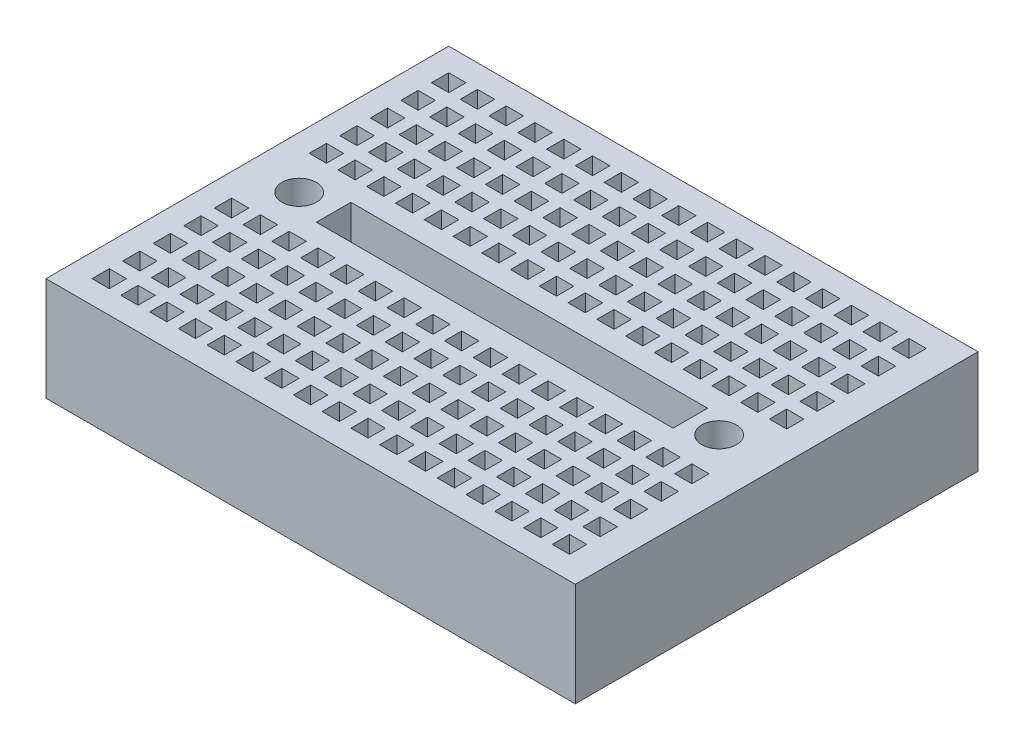
SolidWorks part; units mm, degrees
ref_plane "Front Plane" through (0, 0, 0) normal (0, 0, 1) x (1, 0, 0)
ref_plane "Top Plane" through (0, 0, 0) normal (0, 1, 0) x (1, 0, 0)
ref_plane "Right Plane" through (0, 0, 0) normal (1, 0, 0) x (0, 0, -1)
sketch "Sketch1" plane through (0, 0, 0) normal (0, 1, 0) x (1, 0, 0)
  line L1 (-23, -17.5) -> (23, -17.5)
  line L2 (-23, -17.5) -> (-23, 17.5)
  line L3 (-23, 17.5) -> (23, 17.5)
  line L4 (23, -17.5) -> (23, 17.5)
  point P0 (0, 0)
  dimension "D1" = 46
  dimension "D2" = 35
extrude "Boss-Extrude1" add sketch "Sketch1" along normal blind 9
sketch "Sketch2" plane through (0, 9, 0) normal (0, 1, 0) x (1, 0, 0)
  line L1 (-19.5, 15.5) -> (-21, 15.5)
  line L2 (-21, 15.5) -> (-21, 14)
  line L4 (-15.5, -1.5) -> (15.5, -1.5)
  line L12 (-19.5, 15.5) -> (-19.5, 14)
  line L13 (-19.5, 14) -> (-21, 14)
  line L16 (-17, 15.5) -> (-18.5, 15.5)
  line L17 (-18.5, 15.5) -> (-18.5, 14)
  line L18 (-17, 14) -> (-18.5, 14)
  line L19 (-17, 15.5) -> (-17, 14)
  line L20 (-14.5, 15.5) -> (-16, 15.5)
  line L21 (-16, 15.5) -> (-16, 14)
  line L22 (-14.5, 14) -> (-16, 14)
  line L23 (-14.5, 15.5) -> (-14.5, 14)
  line L24 (-12, 15.5) -> (-13.5, 15.5)
  line L25 (-13.5, 15.5) -> (-13.5, 14)
  line L26 (-12, 14) -> (-13.5, 14)
  line L27 (-12, 15.5) -> (-12, 14)
  line L28 (-9.5, 15.5) -> (-11, 15.5)
  line L29 (-11, 15.5) -> (-11, 14)
  line L30 (-9.5, 14) -> (-11, 14)
  line L31 (-9.5, 15.5) -> (-9.5, 14)
  line L32 (-7, 15.5) -> (-8.5, 15.5)
  line L33 (-8.5, 15.5) -> (-8.5, 14)
  line L34 (-7, 14) -> (-8.5, 14)
  line L35 (-7, 15.5) -> (-7, 14)
  line L36 (-4.5, 15.5) -> (-6, 15.5)
  line L37 (-6, 15.5) -> (-6, 14)
  line L38 (-4.5, 14) -> (-6, 14)
  line L39 (-4.5, 15.5) -> (-4.5, 14)
  line L40 (-2, 15.5) -> (-3.5, 15.5)
  line L41 (-3.5, 15.5) -> (-3.5, 14)
  line L42 (-2, 14) -> (-3.5, 14)
  line L43 (-2, 15.5) -> (-2, 14)
  line L44 (0.5, 15.5) -> (-1, 15.5)
  line L45 (-1, 15.5) -> (-1, 14)
  line L46 (0.5, 14) -> (-1, 14)
  line L47 (0.5, 15.5) -> (0.5, 14)
  line L48 (3, 15.5) -> (1.5, 15.5)
  line L49 (1.5, 15.5) -> (1.5, 14)
  line L50 (3, 14) -> (1.5, 14)
  line L51 (3, 15.5) -> (3, 14)
  line L52 (5.5, 15.5) -> (4, 15.5)
  line L53 (4, 15.5) -> (4, 14)
  line L54 (5.5, 14) -> (4, 14)
  line L55 (5.5, 15.5) -> (5.5, 14)
  line L56 (8, 15.5) -> (6.5, 15.5)
  line L57 (6.5, 15.5) -> (6.5, 14)
  line L58 (8, 14) -> (6.5, 14)
  line L59 (8, 15.5) -> (8, 14)
  line L60 (10.5, 15.5) -> (9, 15.5)
  line L61 (9, 15.5) -> (9, 14)
  line L62 (10.5, 14) -> (9, 14)
  line L63 (10.5, 15.5) -> (10.5, 14)
  line L64 (13, 15.5) -> (11.5, 15.5)
  line L65 (11.5, 15.5) -> (11.5, 14)
  line L66 (13, 14) -> (11.5, 14)
  line L67 (13, 15.5) -> (13, 14)
  line L68 (15.5, 15.5) -> (14, 15.5)
  line L69 (14, 15.5) -> (14, 14)
  line L70 (15.5, 14) -> (14, 14)
  line L71 (15.5, 15.5) -> (15.5, 14)
  line L72 (18, 15.5) -> (16.5, 15.5)
  line L73 (16.5, 15.5) -> (16.5, 14)
  line L74 (18, 14) -> (16.5, 14)
  line L75 (18, 15.5) -> (18, 14)
  line L76 (20.5, 15.5) -> (19, 15.5)
  line L77 (19, 15.5) -> (19, 14)
  line L78 (20.5, 14) -> (19, 14)
  line L79 (20.5, 15.5) -> (20.5, 14)
  line L80 (-17, 12.8426) -> (-18.5, 12.8426)
  line L81 (-18.5, 12.8426) -> (-18.5, 11.3426)
  line L82 (-17, 11.3426) -> (-18.5, 11.3426)
  line L83 (-17, 12.8426) -> (-17, 11.3426)
  line L84 (-14.5, 12.8426) -> (-16, 12.8426)
  line L85 (-16, 12.8426) -> (-16, 11.3426)
  line L86 (-14.5, 11.3426) -> (-16, 11.3426)
  line L87 (-14.5, 12.8426) -> (-14.5, 11.3426)
  line L88 (-12, 12.8426) -> (-13.5, 12.8426)
  line L89 (-13.5, 12.8426) -> (-13.5, 11.3426)
  line L90 (-12, 11.3426) -> (-13.5, 11.3426)
  line L91 (-12, 12.8426) -> (-12, 11.3426)
  line L92 (-9.5, 12.8426) -> (-11, 12.8426)
  line L93 (-11, 12.8426) -> (-11, 11.3426)
  line L94 (-9.5, 11.3426) -> (-11, 11.3426)
  line L95 (-9.5, 12.8426) -> (-9.5, 11.3426)
  line L96 (-7, 12.8426) -> (-8.5, 12.8426)
  line L97 (-8.5, 12.8426) -> (-8.5, 11.3426)
  line L98 (-7, 11.3426) -> (-8.5, 11.3426)
  line L99 (-7, 12.8426) -> (-7, 11.3426)
  line L100 (-4.5, 12.8426) -> (-6, 12.8426)
  line L101 (-6, 12.8426) -> (-6, 11.3426)
  line L102 (-4.5, 11.3426) -> (-6, 11.3426)
  line L103 (-4.5, 12.8426) -> (-4.5, 11.3426)
  line L104 (-2, 12.8426) -> (-3.5, 12.8426)
  line L105 (-3.5, 12.8426) -> (-3.5, 11.3426)
  line L106 (-2, 11.3426) -> (-3.5, 11.3426)
  line L107 (-2, 12.8426) -> (-2, 11.3426)
  line L108 (0.5, 12.8426) -> (-1, 12.8426)
  line L109 (-1, 12.8426) -> (-1, 11.3426)
  line L110 (0.5, 11.3426) -> (-1, 11.3426)
  line L111 (0.5, 12.8426) -> (0.5, 11.3426)
  line L112 (3, 12.8426) -> (1.5, 12.8426)
  line L113 (1.5, 12.8426) -> (1.5, 11.3426)
  line L114 (3, 11.3426) -> (1.5, 11.3426)
  line L115 (3, 12.8426) -> (3, 11.3426)
  line L116 (5.5, 12.8426) -> (4, 12.8426)
  line L117 (4, 12.8426) -> (4, 11.3426)
  line L118 (5.5, 11.3426) -> (4, 11.3426)
  line L119 (5.5, 12.8426) -> (5.5, 11.3426)
  line L120 (8, 12.8426) -> (6.5, 12.8426)
  line L121 (6.5, 12.8426) -> (6.5, 11.3426)
  line L122 (8, 11.3426) -> (6.5, 11.3426)
  line L123 (8, 12.8426) -> (8, 11.3426)
  line L124 (10.5, 12.8426) -> (9, 12.8426)
  line L125 (9, 12.8426) -> (9, 11.3426)
  line L126 (10.5, 11.3426) -> (9, 11.3426)
  line L127 (10.5, 12.8426) -> (10.5, 11.3426)
  line L128 (13, 12.8426) -> (11.5, 12.8426)
  line L129 (11.5, 12.8426) -> (11.5, 11.3426)
  line L130 (13, 11.3426) -> (11.5, 11.3426)
  line L131 (13, 12.8426) -> (13, 11.3426)
  line L132 (15.5, 12.8426) -> (14, 12.8426)
  line L133 (14, 12.8426) -> (14, 11.3426)
  line L134 (15.5, 11.3426) -> (14, 11.3426)
  line L135 (15.5, 12.8426) -> (15.5, 11.3426)
  line L136 (18, 12.8426) -> (16.5, 12.8426)
  line L137 (16.5, 12.8426) -> (16.5, 11.3426)
  line L138 (18, 11.3426) -> (16.5, 11.3426)
  line L139 (18, 12.8426) -> (18, 11.3426)
  line L140 (20.5, 12.8426) -> (19, 12.8426)
  line L141 (19, 12.8426) -> (19, 11.3426)
  line L142 (20.5, 11.3426) -> (19, 11.3426)
  line L143 (20.5, 12.8426) -> (20.5, 11.3426)
  line L144 (-17, 10.1851) -> (-18.5, 10.1851)
  line L145 (-18.5, 10.1851) -> (-18.5, 8.6851)
  line L146 (-17, 8.6851) -> (-18.5, 8.6851)
  line L147 (-17, 10.1851) -> (-17, 8.6851)
  line L148 (-14.5, 10.1851) -> (-16, 10.1851)
  line L149 (-16, 10.1851) -> (-16, 8.6851)
  line L150 (-14.5, 8.6851) -> (-16, 8.6851)
  line L151 (-14.5, 10.1851) -> (-14.5, 8.6851)
  line L152 (-12, 10.1851) -> (-13.5, 10.1851)
  line L153 (-13.5, 10.1851) -> (-13.5, 8.6851)
  line L154 (-12, 8.6851) -> (-13.5, 8.6851)
  line L155 (-12, 10.1851) -> (-12, 8.6851)
  line L156 (-9.5, 10.1851) -> (-11, 10.1851)
  line L157 (-11, 10.1851) -> (-11, 8.6851)
  line L158 (-9.5, 8.6851) -> (-11, 8.6851)
  line L159 (-9.5, 10.1851) -> (-9.5, 8.6851)
  line L160 (-7, 10.1851) -> (-8.5, 10.1851)
  line L161 (-8.5, 10.1851) -> (-8.5, 8.6851)
  line L162 (-7, 8.6851) -> (-8.5, 8.6851)
  line L163 (-7, 10.1851) -> (-7, 8.6851)
  line L164 (-4.5, 10.1851) -> (-6, 10.1851)
  line L165 (-6, 10.1851) -> (-6, 8.6851)
  line L166 (-4.5, 8.6851) -> (-6, 8.6851)
  line L167 (-4.5, 10.1851) -> (-4.5, 8.6851)
  line L168 (-2, 10.1851) -> (-3.5, 10.1851)
  line L169 (-3.5, 10.1851) -> (-3.5, 8.6851)
  line L170 (-2, 8.6851) -> (-3.5, 8.6851)
  line L171 (-2, 10.1851) -> (-2, 8.6851)
  line L172 (0.5, 10.1851) -> (-1, 10.1851)
  line L173 (-1, 10.1851) -> (-1, 8.6851)
  line L174 (0.5, 8.6851) -> (-1, 8.6851)
  line L175 (0.5, 10.1851) -> (0.5, 8.6851)
  line L176 (3, 10.1851) -> (1.5, 10.1851)
  line L177 (1.5, 10.1851) -> (1.5, 8.6851)
  line L178 (3, 8.6851) -> (1.5, 8.6851)
  line L179 (3, 10.1851) -> (3, 8.6851)
  line L180 (5.5, 10.1851) -> (4, 10.1851)
  line L181 (4, 10.1851) -> (4, 8.6851)
  line L182 (5.5, 8.6851) -> (4, 8.6851)
  line L183 (5.5, 10.1851) -> (5.5, 8.6851)
  line L184 (8, 10.1851) -> (6.5, 10.1851)
  line L185 (6.5, 10.1851) -> (6.5, 8.6851)
  line L186 (8, 8.6851) -> (6.5, 8.6851)
  line L187 (8, 10.1851) -> (8, 8.6851)
  line L188 (10.5, 10.1851) -> (9, 10.1851)
  line L189 (9, 10.1851) -> (9, 8.6851)
  line L190 (10.5, 8.6851) -> (9, 8.6851)
  line L191 (10.5, 10.1851) -> (10.5, 8.6851)
  line L192 (13, 10.1851) -> (11.5, 10.1851)
  line L193 (11.5, 10.1851) -> (11.5, 8.6851)
  line L194 (13, 8.6851) -> (11.5, 8.6851)
  line L195 (13, 10.1851) -> (13, 8.6851)
  line L196 (15.5, 10.1851) -> (14, 10.1851)
  line L197 (14, 10.1851) -> (14, 8.6851)
  line L198 (15.5, 8.6851) -> (14, 8.6851)
  line L199 (15.5, 10.1851) -> (15.5, 8.6851)
  line L200 (18, 10.1851) -> (16.5, 10.1851)
  line L201 (16.5, 10.1851) -> (16.5, 8.6851)
  line L202 (18, 8.6851) -> (16.5, 8.6851)
  line L203 (18, 10.1851) -> (18, 8.6851)
  line L204 (20.5, 10.1851) -> (19, 10.1851)
  line L205 (19, 10.1851) -> (19, 8.6851)
  line L206 (20.5, 8.6851) -> (19, 8.6851)
  line L207 (20.5, 10.1851) -> (20.5, 8.6851)
  line L208 (-17, 7.5277) -> (-18.5, 7.5277)
  line L209 (-18.5, 7.5277) -> (-18.5, 6.0277)
  line L210 (-17, 6.0277) -> (-18.5, 6.0277)
  line L211 (-17, 7.5277) -> (-17, 6.0277)
  line L212 (-14.5, 7.5277) -> (-16, 7.5277)
  line L213 (-16, 7.5277) -> (-16, 6.0277)
  line L214 (-14.5, 6.0277) -> (-16, 6.0277)
  line L215 (-14.5, 7.5277) -> (-14.5, 6.0277)
  line L216 (-12, 7.5277) -> (-13.5, 7.5277)
  line L217 (-13.5, 7.5277) -> (-13.5, 6.0277)
  line L218 (-12, 6.0277) -> (-13.5, 6.0277)
  line L219 (-12, 7.5277) -> (-12, 6.0277)
  line L220 (-9.5, 7.5277) -> (-11, 7.5277)
  line L221 (-11, 7.5277) -> (-11, 6.0277)
  line L222 (-9.5, 6.0277) -> (-11, 6.0277)
  line L223 (-9.5, 7.5277) -> (-9.5, 6.0277)
  line L224 (-7, 7.5277) -> (-8.5, 7.5277)
  line L225 (-8.5, 7.5277) -> (-8.5, 6.0277)
  line L226 (-7, 6.0277) -> (-8.5, 6.0277)
  line L227 (-7, 7.5277) -> (-7, 6.0277)
  line L228 (-4.5, 7.5277) -> (-6, 7.5277)
  line L229 (-6, 7.5277) -> (-6, 6.0277)
  line L230 (-4.5, 6.0277) -> (-6, 6.0277)
  line L231 (-4.5, 7.5277) -> (-4.5, 6.0277)
  line L232 (-2, 7.5277) -> (-3.5, 7.5277)
  line L233 (-3.5, 7.5277) -> (-3.5, 6.0277)
  line L234 (-2, 6.0277) -> (-3.5, 6.0277)
  line L235 (-2, 7.5277) -> (-2, 6.0277)
  line L236 (0.5, 7.5277) -> (-1, 7.5277)
  line L237 (-1, 7.5277) -> (-1, 6.0277)
  line L238 (0.5, 6.0277) -> (-1, 6.0277)
  line L239 (0.5, 7.5277) -> (0.5, 6.0277)
  line L240 (3, 7.5277) -> (1.5, 7.5277)
  line L241 (1.5, 7.5277) -> (1.5, 6.0277)
  line L242 (3, 6.0277) -> (1.5, 6.0277)
  line L243 (3, 7.5277) -> (3, 6.0277)
  line L244 (5.5, 7.5277) -> (4, 7.5277)
  line L245 (4, 7.5277) -> (4, 6.0277)
  line L246 (5.5, 6.0277) -> (4, 6.0277)
  line L247 (5.5, 7.5277) -> (5.5, 6.0277)
  line L248 (8, 7.5277) -> (6.5, 7.5277)
  line L249 (6.5, 7.5277) -> (6.5, 6.0277)
  line L250 (8, 6.0277) -> (6.5, 6.0277)
  line L251 (8, 7.5277) -> (8, 6.0277)
  line L252 (10.5, 7.5277) -> (9, 7.5277)
  line L253 (9, 7.5277) -> (9, 6.0277)
  line L254 (10.5, 6.0277) -> (9, 6.0277)
  line L255 (10.5, 7.5277) -> (10.5, 6.0277)
  line L256 (13, 7.5277) -> (11.5, 7.5277)
  line L257 (11.5, 7.5277) -> (11.5, 6.0277)
  line L258 (13, 6.0277) -> (11.5, 6.0277)
  line L259 (13, 7.5277) -> (13, 6.0277)
  line L260 (15.5, 7.5277) -> (14, 7.5277)
  line L261 (14, 7.5277) -> (14, 6.0277)
  line L262 (15.5, 6.0277) -> (14, 6.0277)
  line L263 (15.5, 7.5277) -> (15.5, 6.0277)
  line L264 (18, 7.5277) -> (16.5, 7.5277)
  line L265 (16.5, 7.5277) -> (16.5, 6.0277)
  line L266 (18, 6.0277) -> (16.5, 6.0277)
  line L267 (18, 7.5277) -> (18, 6.0277)
  line L268 (20.5, 7.5277) -> (19, 7.5277)
  line L269 (19, 7.5277) -> (19, 6.0277)
  line L270 (20.5, 6.0277) -> (19, 6.0277)
  line L271 (20.5, 7.5277) -> (20.5, 6.0277)
  line L272 (-17, 4.8702) -> (-18.5, 4.8702)
  line L273 (-18.5, 4.8702) -> (-18.5, 3.3702)
  line L274 (-17, 3.3702) -> (-18.5, 3.3702)
  line L275 (-17, 4.8702) -> (-17, 3.3702)
  line L276 (-14.5, 4.8702) -> (-16, 4.8702)
  line L277 (-16, 4.8702) -> (-16, 3.3702)
  line L278 (-14.5, 3.3702) -> (-16, 3.3702)
  line L279 (-14.5, 4.8702) -> (-14.5, 3.3702)
  line L280 (-12, 4.8702) -> (-13.5, 4.8702)
  line L281 (-13.5, 4.8702) -> (-13.5, 3.3702)
  line L282 (-12, 3.3702) -> (-13.5, 3.3702)
  line L283 (-12, 4.8702) -> (-12, 3.3702)
  line L284 (-9.5, 4.8702) -> (-11, 4.8702)
  line L285 (-11, 4.8702) -> (-11, 3.3702)
  line L286 (-9.5, 3.3702) -> (-11, 3.3702)
  line L287 (-9.5, 4.8702) -> (-9.5, 3.3702)
  line L288 (-7, 4.8702) -> (-8.5, 4.8702)
  line L289 (-8.5, 4.8702) -> (-8.5, 3.3702)
  line L290 (-7, 3.3702) -> (-8.5, 3.3702)
  line L291 (-7, 4.8702) -> (-7, 3.3702)
  line L292 (-4.5, 4.8702) -> (-6, 4.8702)
  line L293 (-6, 4.8702) -> (-6, 3.3702)
  line L294 (-4.5, 3.3702) -> (-6, 3.3702)
  line L295 (-4.5, 4.8702) -> (-4.5, 3.3702)
  line L296 (-2, 4.8702) -> (-3.5, 4.8702)
  line L297 (-3.5, 4.8702) -> (-3.5, 3.3702)
  line L298 (-2, 3.3702) -> (-3.5, 3.3702)
  line L299 (-2, 4.8702) -> (-2, 3.3702)
  line L300 (0.5, 4.8702) -> (-1, 4.8702)
  line L301 (-1, 4.8702) -> (-1, 3.3702)
  line L302 (0.5, 3.3702) -> (-1, 3.3702)
  line L303 (0.5, 4.8702) -> (0.5, 3.3702)
  line L304 (3, 4.8702) -> (1.5, 4.8702)
  line L305 (1.5, 4.8702) -> (1.5, 3.3702)
  line L306 (3, 3.3702) -> (1.5, 3.3702)
  line L307 (3, 4.8702) -> (3, 3.3702)
  line L308 (5.5, 4.8702) -> (4, 4.8702)
  line L309 (4, 4.8702) -> (4, 3.3702)
  line L310 (5.5, 3.3702) -> (4, 3.3702)
  line L311 (5.5, 4.8702) -> (5.5, 3.3702)
  line L312 (8, 4.8702) -> (6.5, 4.8702)
  line L313 (6.5, 4.8702) -> (6.5, 3.3702)
  line L314 (8, 3.3702) -> (6.5, 3.3702)
  line L315 (8, 4.8702) -> (8, 3.3702)
  line L316 (10.5, 4.8702) -> (9, 4.8702)
  line L317 (9, 4.8702) -> (9, 3.3702)
  line L318 (10.5, 3.3702) -> (9, 3.3702)
  line L319 (10.5, 4.8702) -> (10.5, 3.3702)
  line L320 (13, 4.8702) -> (11.5, 4.8702)
  line L321 (11.5, 4.8702) -> (11.5, 3.3702)
  line L322 (13, 3.3702) -> (11.5, 3.3702)
  line L323 (13, 4.8702) -> (13, 3.3702)
  line L324 (15.5, 4.8702) -> (14, 4.8702)
  line L325 (14, 4.8702) -> (14, 3.3702)
  line L326 (15.5, 3.3702) -> (14, 3.3702)
  line L327 (15.5, 4.8702) -> (15.5, 3.3702)
  line L328 (18, 4.8702) -> (16.5, 4.8702)
  line L329 (16.5, 4.8702) -> (16.5, 3.3702)
  line L330 (18, 3.3702) -> (16.5, 3.3702)
  line L331 (18, 4.8702) -> (18, 3.3702)
  line L332 (20.5, 4.8702) -> (19, 4.8702)
  line L333 (19, 4.8702) -> (19, 3.3702)
  line L334 (20.5, 3.3702) -> (19, 3.3702)
  line L335 (20.5, 4.8702) -> (20.5, 3.3702)
  line L336 (-19.5, 12.8426) -> (-21, 12.8426)
  line L337 (-21, 12.8426) -> (-21, 11.3426)
  line L338 (-19.5, 11.3426) -> (-21, 11.3426)
  line L339 (-19.5, 12.8426) -> (-19.5, 11.3426)
  line L340 (-19.5, 10.1851) -> (-21, 10.1851)
  line L341 (-21, 10.1851) -> (-21, 8.6851)
  line L342 (-19.5, 8.6851) -> (-21, 8.6851)
  line L343 (-19.5, 10.1851) -> (-19.5, 8.6851)
  line L344 (-19.5, 7.5277) -> (-21, 7.5277)
  line L345 (-21, 7.5277) -> (-21, 6.0277)
  line L346 (-19.5, 6.0277) -> (-21, 6.0277)
  line L347 (-19.5, 7.5277) -> (-19.5, 6.0277)
  line L348 (-19.5, 4.8702) -> (-21, 4.8702)
  line L349 (-21, 4.8702) -> (-21, 3.3702)
  line L350 (-19.5, 3.3702) -> (-21, 3.3702)
  line L351 (-19.5, 4.8702) -> (-19.5, 3.3702)
  line L356 (-15.5, -1.5) -> (-15.5, 1.5)
  line L357 (-15.5, 1.5) -> (15.5, 1.5)
  line L358 (15.5, -1.5) -> (15.5, 1.5)
  line L363 (-19.5, -4.8702) -> (-19.5, -3.3702)
  line L364 (-19.5, -3.3702) -> (-21, -3.3702)
  line L365 (-21, -4.8702) -> (-21, -3.3702)
  line L366 (-19.5, -4.8702) -> (-21, -4.8702)
  line L367 (-19.5, -7.5277) -> (-19.5, -6.0277)
  line L368 (-19.5, -6.0277) -> (-21, -6.0277)
  line L369 (-21, -7.5277) -> (-21, -6.0277)
  line L370 (-19.5, -7.5277) -> (-21, -7.5277)
  line L371 (-19.5, -10.1851) -> (-19.5, -8.6851)
  line L372 (-19.5, -8.6851) -> (-21, -8.6851)
  line L373 (-21, -10.1851) -> (-21, -8.6851)
  line L374 (-19.5, -10.1851) -> (-21, -10.1851)
  line L375 (-19.5, -12.8426) -> (-19.5, -11.3426)
  line L376 (-19.5, -11.3426) -> (-21, -11.3426)
  line L377 (-21, -12.8426) -> (-21, -11.3426)
  line L378 (-19.5, -12.8426) -> (-21, -12.8426)
  line L379 (20.5, -4.8702) -> (20.5, -3.3702)
  line L380 (20.5, -3.3702) -> (19, -3.3702)
  line L381 (19, -4.8702) -> (19, -3.3702)
  line L382 (20.5, -4.8702) -> (19, -4.8702)
  line L383 (18, -4.8702) -> (18, -3.3702)
  line L384 (18, -3.3702) -> (16.5, -3.3702)
  line L385 (16.5, -4.8702) -> (16.5, -3.3702)
  line L386 (18, -4.8702) -> (16.5, -4.8702)
  line L387 (15.5, -4.8702) -> (15.5, -3.3702)
  line L388 (15.5, -3.3702) -> (14, -3.3702)
  line L389 (14, -4.8702) -> (14, -3.3702)
  line L390 (15.5, -4.8702) -> (14, -4.8702)
  line L391 (13, -4.8702) -> (13, -3.3702)
  line L392 (13, -3.3702) -> (11.5, -3.3702)
  line L393 (11.5, -4.8702) -> (11.5, -3.3702)
  line L394 (13, -4.8702) -> (11.5, -4.8702)
  line L395 (10.5, -4.8702) -> (10.5, -3.3702)
  line L396 (10.5, -3.3702) -> (9, -3.3702)
  line L397 (9, -4.8702) -> (9, -3.3702)
  line L398 (10.5, -4.8702) -> (9, -4.8702)
  line L399 (8, -4.8702) -> (8, -3.3702)
  line L400 (8, -3.3702) -> (6.5, -3.3702)
  line L401 (6.5, -4.8702) -> (6.5, -3.3702)
  line L402 (8, -4.8702) -> (6.5, -4.8702)
  line L403 (5.5, -4.8702) -> (5.5, -3.3702)
  line L404 (5.5, -3.3702) -> (4, -3.3702)
  line L405 (4, -4.8702) -> (4, -3.3702)
  line L406 (5.5, -4.8702) -> (4, -4.8702)
  line L407 (3, -4.8702) -> (3, -3.3702)
  line L408 (3, -3.3702) -> (1.5, -3.3702)
  line L409 (1.5, -4.8702) -> (1.5, -3.3702)
  line L410 (3, -4.8702) -> (1.5, -4.8702)
  line L411 (0.5, -4.8702) -> (0.5, -3.3702)
  line L412 (0.5, -3.3702) -> (-1, -3.3702)
  line L413 (-1, -4.8702) -> (-1, -3.3702)
  line L414 (0.5, -4.8702) -> (-1, -4.8702)
  line L415 (-2, -4.8702) -> (-2, -3.3702)
  line L416 (-2, -3.3702) -> (-3.5, -3.3702)
  line L417 (-3.5, -4.8702) -> (-3.5, -3.3702)
  line L418 (-2, -4.8702) -> (-3.5, -4.8702)
  line L419 (-4.5, -4.8702) -> (-4.5, -3.3702)
  line L420 (-4.5, -3.3702) -> (-6, -3.3702)
  line L421 (-6, -4.8702) -> (-6, -3.3702)
  line L422 (-4.5, -4.8702) -> (-6, -4.8702)
  line L423 (-7, -4.8702) -> (-7, -3.3702)
  line L424 (-7, -3.3702) -> (-8.5, -3.3702)
  line L425 (-8.5, -4.8702) -> (-8.5, -3.3702)
  line L426 (-7, -4.8702) -> (-8.5, -4.8702)
  line L427 (-9.5, -4.8702) -> (-9.5, -3.3702)
  line L428 (-9.5, -3.3702) -> (-11, -3.3702)
  line L429 (-11, -4.8702) -> (-11, -3.3702)
  line L430 (-9.5, -4.8702) -> (-11, -4.8702)
  line L431 (-12, -4.8702) -> (-12, -3.3702)
  line L432 (-12, -3.3702) -> (-13.5, -3.3702)
  line L433 (-13.5, -4.8702) -> (-13.5, -3.3702)
  line L434 (-12, -4.8702) -> (-13.5, -4.8702)
  line L435 (-14.5, -4.8702) -> (-14.5, -3.3702)
  line L436 (-14.5, -3.3702) -> (-16, -3.3702)
  line L437 (-16, -4.8702) -> (-16, -3.3702)
  line L438 (-14.5, -4.8702) -> (-16, -4.8702)
  line L439 (-17, -4.8702) -> (-17, -3.3702)
  line L440 (-17, -3.3702) -> (-18.5, -3.3702)
  line L441 (-18.5, -4.8702) -> (-18.5, -3.3702)
  line L442 (-17, -4.8702) -> (-18.5, -4.8702)
  line L443 (20.5, -7.5277) -> (20.5, -6.0277)
  line L444 (20.5, -6.0277) -> (19, -6.0277)
  line L445 (19, -7.5277) -> (19, -6.0277)
  line L446 (20.5, -7.5277) -> (19, -7.5277)
  line L447 (18, -7.5277) -> (18, -6.0277)
  line L448 (18, -6.0277) -> (16.5, -6.0277)
  line L449 (16.5, -7.5277) -> (16.5, -6.0277)
  line L450 (18, -7.5277) -> (16.5, -7.5277)
  line L451 (15.5, -7.5277) -> (15.5, -6.0277)
  line L452 (15.5, -6.0277) -> (14, -6.0277)
  line L453 (14, -7.5277) -> (14, -6.0277)
  line L454 (15.5, -7.5277) -> (14, -7.5277)
  line L455 (13, -7.5277) -> (13, -6.0277)
  line L456 (13, -6.0277) -> (11.5, -6.0277)
  line L457 (11.5, -7.5277) -> (11.5, -6.0277)
  line L458 (13, -7.5277) -> (11.5, -7.5277)
  line L459 (10.5, -7.5277) -> (10.5, -6.0277)
  line L460 (10.5, -6.0277) -> (9, -6.0277)
  line L461 (9, -7.5277) -> (9, -6.0277)
  line L462 (10.5, -7.5277) -> (9, -7.5277)
  line L463 (8, -7.5277) -> (8, -6.0277)
  line L464 (8, -6.0277) -> (6.5, -6.0277)
  line L465 (6.5, -7.5277) -> (6.5, -6.0277)
  line L466 (8, -7.5277) -> (6.5, -7.5277)
  line L467 (5.5, -7.5277) -> (5.5, -6.0277)
  line L468 (5.5, -6.0277) -> (4, -6.0277)
  line L469 (4, -7.5277) -> (4, -6.0277)
  line L470 (5.5, -7.5277) -> (4, -7.5277)
  line L471 (3, -7.5277) -> (3, -6.0277)
  line L472 (3, -6.0277) -> (1.5, -6.0277)
  line L473 (1.5, -7.5277) -> (1.5, -6.0277)
  line L474 (3, -7.5277) -> (1.5, -7.5277)
  line L475 (0.5, -7.5277) -> (0.5, -6.0277)
  line L476 (0.5, -6.0277) -> (-1, -6.0277)
  line L477 (-1, -7.5277) -> (-1, -6.0277)
  line L478 (0.5, -7.5277) -> (-1, -7.5277)
  line L479 (-2, -7.5277) -> (-2, -6.0277)
  line L480 (-2, -6.0277) -> (-3.5, -6.0277)
  line L481 (-3.5, -7.5277) -> (-3.5, -6.0277)
  line L482 (-2, -7.5277) -> (-3.5, -7.5277)
  line L483 (-4.5, -7.5277) -> (-4.5, -6.0277)
  line L484 (-4.5, -6.0277) -> (-6, -6.0277)
  line L485 (-6, -7.5277) -> (-6, -6.0277)
  line L486 (-4.5, -7.5277) -> (-6, -7.5277)
  line L487 (-7, -7.5277) -> (-7, -6.0277)
  line L488 (-7, -6.0277) -> (-8.5, -6.0277)
  line L489 (-8.5, -7.5277) -> (-8.5, -6.0277)
  line L490 (-7, -7.5277) -> (-8.5, -7.5277)
  line L491 (-9.5, -7.5277) -> (-9.5, -6.0277)
  line L492 (-9.5, -6.0277) -> (-11, -6.0277)
  line L493 (-11, -7.5277) -> (-11, -6.0277)
  line L494 (-9.5, -7.5277) -> (-11, -7.5277)
  line L495 (-12, -7.5277) -> (-12, -6.0277)
  line L496 (-12, -6.0277) -> (-13.5, -6.0277)
  line L497 (-13.5, -7.5277) -> (-13.5, -6.0277)
  line L498 (-12, -7.5277) -> (-13.5, -7.5277)
  line L499 (-14.5, -7.5277) -> (-14.5, -6.0277)
  line L500 (-14.5, -6.0277) -> (-16, -6.0277)
  line L501 (-16, -7.5277) -> (-16, -6.0277)
  line L502 (-14.5, -7.5277) -> (-16, -7.5277)
  line L503 (-17, -7.5277) -> (-17, -6.0277)
  line L504 (-17, -6.0277) -> (-18.5, -6.0277)
  line L505 (-18.5, -7.5277) -> (-18.5, -6.0277)
  line L506 (-17, -7.5277) -> (-18.5, -7.5277)
  line L507 (20.5, -10.1851) -> (20.5, -8.6851)
  line L508 (20.5, -8.6851) -> (19, -8.6851)
  line L509 (19, -10.1851) -> (19, -8.6851)
  line L510 (20.5, -10.1851) -> (19, -10.1851)
  line L511 (18, -10.1851) -> (18, -8.6851)
  line L512 (18, -8.6851) -> (16.5, -8.6851)
  line L513 (16.5, -10.1851) -> (16.5, -8.6851)
  line L514 (18, -10.1851) -> (16.5, -10.1851)
  line L515 (15.5, -10.1851) -> (15.5, -8.6851)
  line L516 (15.5, -8.6851) -> (14, -8.6851)
  line L517 (14, -10.1851) -> (14, -8.6851)
  line L518 (15.5, -10.1851) -> (14, -10.1851)
  line L519 (13, -10.1851) -> (13, -8.6851)
  line L520 (13, -8.6851) -> (11.5, -8.6851)
  line L521 (11.5, -10.1851) -> (11.5, -8.6851)
  line L522 (13, -10.1851) -> (11.5, -10.1851)
  line L523 (10.5, -10.1851) -> (10.5, -8.6851)
  line L524 (10.5, -8.6851) -> (9, -8.6851)
  line L525 (9, -10.1851) -> (9, -8.6851)
  line L526 (10.5, -10.1851) -> (9, -10.1851)
  line L527 (8, -10.1851) -> (8, -8.6851)
  line L528 (8, -8.6851) -> (6.5, -8.6851)
  line L529 (6.5, -10.1851) -> (6.5, -8.6851)
  line L530 (8, -10.1851) -> (6.5, -10.1851)
  line L531 (5.5, -10.1851) -> (5.5, -8.6851)
  line L532 (5.5, -8.6851) -> (4, -8.6851)
  line L533 (4, -10.1851) -> (4, -8.6851)
  line L534 (5.5, -10.1851) -> (4, -10.1851)
  line L535 (3, -10.1851) -> (3, -8.6851)
  line L536 (3, -8.6851) -> (1.5, -8.6851)
  line L537 (1.5, -10.1851) -> (1.5, -8.6851)
  line L538 (3, -10.1851) -> (1.5, -10.1851)
  line L539 (0.5, -10.1851) -> (0.5, -8.6851)
  line L540 (0.5, -8.6851) -> (-1, -8.6851)
  line L541 (-1, -10.1851) -> (-1, -8.6851)
  line L542 (0.5, -10.1851) -> (-1, -10.1851)
  line L543 (-2, -10.1851) -> (-2, -8.6851)
  line L544 (-2, -8.6851) -> (-3.5, -8.6851)
  line L545 (-3.5, -10.1851) -> (-3.5, -8.6851)
  line L546 (-2, -10.1851) -> (-3.5, -10.1851)
  line L547 (-4.5, -10.1851) -> (-4.5, -8.6851)
  line L548 (-4.5, -8.6851) -> (-6, -8.6851)
  line L549 (-6, -10.1851) -> (-6, -8.6851)
  line L550 (-4.5, -10.1851) -> (-6, -10.1851)
  line L551 (-7, -10.1851) -> (-7, -8.6851)
  line L552 (-7, -8.6851) -> (-8.5, -8.6851)
  line L553 (-8.5, -10.1851) -> (-8.5, -8.6851)
  line L554 (-7, -10.1851) -> (-8.5, -10.1851)
  line L555 (-9.5, -10.1851) -> (-9.5, -8.6851)
  line L556 (-9.5, -8.6851) -> (-11, -8.6851)
  line L557 (-11, -10.1851) -> (-11, -8.6851)
  line L558 (-9.5, -10.1851) -> (-11, -10.1851)
  line L559 (-12, -10.1851) -> (-12, -8.6851)
  line L560 (-12, -8.6851) -> (-13.5, -8.6851)
  line L561 (-13.5, -10.1851) -> (-13.5, -8.6851)
  line L562 (-12, -10.1851) -> (-13.5, -10.1851)
  line L563 (-14.5, -10.1851) -> (-14.5, -8.6851)
  line L564 (-14.5, -8.6851) -> (-16, -8.6851)
  line L565 (-16, -10.1851) -> (-16, -8.6851)
  line L566 (-14.5, -10.1851) -> (-16, -10.1851)
  line L567 (-17, -10.1851) -> (-17, -8.6851)
  line L568 (-17, -8.6851) -> (-18.5, -8.6851)
  line L569 (-18.5, -10.1851) -> (-18.5, -8.6851)
  line L570 (-17, -10.1851) -> (-18.5, -10.1851)
  line L571 (20.5, -12.8426) -> (20.5, -11.3426)
  line L572 (20.5, -11.3426) -> (19, -11.3426)
  line L573 (19, -12.8426) -> (19, -11.3426)
  line L574 (20.5, -12.8426) -> (19, -12.8426)
  line L575 (18, -12.8426) -> (18, -11.3426)
  line L576 (18, -11.3426) -> (16.5, -11.3426)
  line L577 (16.5, -12.8426) -> (16.5, -11.3426)
  line L578 (18, -12.8426) -> (16.5, -12.8426)
  line L579 (15.5, -12.8426) -> (15.5, -11.3426)
  line L580 (15.5, -11.3426) -> (14, -11.3426)
  line L581 (14, -12.8426) -> (14, -11.3426)
  line L582 (15.5, -12.8426) -> (14, -12.8426)
  line L583 (13, -12.8426) -> (13, -11.3426)
  line L584 (13, -11.3426) -> (11.5, -11.3426)
  line L585 (11.5, -12.8426) -> (11.5, -11.3426)
  line L586 (13, -12.8426) -> (11.5, -12.8426)
  line L587 (10.5, -12.8426) -> (10.5, -11.3426)
  line L588 (10.5, -11.3426) -> (9, -11.3426)
  line L589 (9, -12.8426) -> (9, -11.3426)
  line L590 (10.5, -12.8426) -> (9, -12.8426)
  line L591 (8, -12.8426) -> (8, -11.3426)
  line L592 (8, -11.3426) -> (6.5, -11.3426)
  line L593 (6.5, -12.8426) -> (6.5, -11.3426)
  line L594 (8, -12.8426) -> (6.5, -12.8426)
  line L595 (5.5, -12.8426) -> (5.5, -11.3426)
  line L596 (5.5, -11.3426) -> (4, -11.3426)
  line L597 (4, -12.8426) -> (4, -11.3426)
  line L598 (5.5, -12.8426) -> (4, -12.8426)
  line L599 (3, -12.8426) -> (3, -11.3426)
  line L600 (3, -11.3426) -> (1.5, -11.3426)
  line L601 (1.5, -12.8426) -> (1.5, -11.3426)
  line L602 (3, -12.8426) -> (1.5, -12.8426)
  line L603 (0.5, -12.8426) -> (0.5, -11.3426)
  line L604 (0.5, -11.3426) -> (-1, -11.3426)
  line L605 (-1, -12.8426) -> (-1, -11.3426)
  line L606 (0.5, -12.8426) -> (-1, -12.8426)
  line L607 (-2, -12.8426) -> (-2, -11.3426)
  line L608 (-2, -11.3426) -> (-3.5, -11.3426)
  line L609 (-3.5, -12.8426) -> (-3.5, -11.3426)
  line L610 (-2, -12.8426) -> (-3.5, -12.8426)
  line L611 (-4.5, -12.8426) -> (-4.5, -11.3426)
  line L612 (-4.5, -11.3426) -> (-6, -11.3426)
  line L613 (-6, -12.8426) -> (-6, -11.3426)
  line L614 (-4.5, -12.8426) -> (-6, -12.8426)
  line L615 (-7, -12.8426) -> (-7, -11.3426)
  line L616 (-7, -11.3426) -> (-8.5, -11.3426)
  line L617 (-8.5, -12.8426) -> (-8.5, -11.3426)
  line L618 (-7, -12.8426) -> (-8.5, -12.8426)
  line L619 (-9.5, -12.8426) -> (-9.5, -11.3426)
  line L620 (-9.5, -11.3426) -> (-11, -11.3426)
  line L621 (-11, -12.8426) -> (-11, -11.3426)
  line L622 (-9.5, -12.8426) -> (-11, -12.8426)
  line L623 (-12, -12.8426) -> (-12, -11.3426)
  line L624 (-12, -11.3426) -> (-13.5, -11.3426)
  line L625 (-13.5, -12.8426) -> (-13.5, -11.3426)
  line L626 (-12, -12.8426) -> (-13.5, -12.8426)
  line L627 (-14.5, -12.8426) -> (-14.5, -11.3426)
  line L628 (-14.5, -11.3426) -> (-16, -11.3426)
  line L629 (-16, -12.8426) -> (-16, -11.3426)
  line L630 (-14.5, -12.8426) -> (-16, -12.8426)
  line L631 (-17, -12.8426) -> (-17, -11.3426)
  line L632 (-17, -11.3426) -> (-18.5, -11.3426)
  line L633 (-18.5, -12.8426) -> (-18.5, -11.3426)
  line L634 (-17, -12.8426) -> (-18.5, -12.8426)
  line L635 (20.5, -15.5) -> (20.5, -14)
  line L636 (20.5, -14) -> (19, -14)
  line L637 (19, -15.5) -> (19, -14)
  line L638 (20.5, -15.5) -> (19, -15.5)
  line L639 (18, -15.5) -> (18, -14)
  line L640 (18, -14) -> (16.5, -14)
  line L641 (16.5, -15.5) -> (16.5, -14)
  line L642 (18, -15.5) -> (16.5, -15.5)
  line L643 (15.5, -15.5) -> (15.5, -14)
  line L644 (15.5, -14) -> (14, -14)
  line L645 (14, -15.5) -> (14, -14)
  line L646 (15.5, -15.5) -> (14, -15.5)
  line L647 (13, -15.5) -> (13, -14)
  line L648 (13, -14) -> (11.5, -14)
  line L649 (11.5, -15.5) -> (11.5, -14)
  line L650 (13, -15.5) -> (11.5, -15.5)
  line L651 (10.5, -15.5) -> (10.5, -14)
  line L652 (10.5, -14) -> (9, -14)
  line L653 (9, -15.5) -> (9, -14)
  line L654 (10.5, -15.5) -> (9, -15.5)
  line L655 (8, -15.5) -> (8, -14)
  line L656 (8, -14) -> (6.5, -14)
  line L657 (6.5, -15.5) -> (6.5, -14)
  line L658 (8, -15.5) -> (6.5, -15.5)
  line L659 (5.5, -15.5) -> (5.5, -14)
  line L660 (5.5, -14) -> (4, -14)
  line L661 (4, -15.5) -> (4, -14)
  line L662 (5.5, -15.5) -> (4, -15.5)
  line L663 (3, -15.5) -> (3, -14)
  line L664 (3, -14) -> (1.5, -14)
  line L665 (1.5, -15.5) -> (1.5, -14)
  line L666 (3, -15.5) -> (1.5, -15.5)
  line L667 (0.5, -15.5) -> (0.5, -14)
  line L668 (0.5, -14) -> (-1, -14)
  line L669 (-1, -15.5) -> (-1, -14)
  line L670 (0.5, -15.5) -> (-1, -15.5)
  line L671 (-2, -15.5) -> (-2, -14)
  line L672 (-2, -14) -> (-3.5, -14)
  line L673 (-3.5, -15.5) -> (-3.5, -14)
  line L674 (-2, -15.5) -> (-3.5, -15.5)
  line L675 (-4.5, -15.5) -> (-4.5, -14)
  line L676 (-4.5, -14) -> (-6, -14)
  line L677 (-6, -15.5) -> (-6, -14)
  line L678 (-4.5, -15.5) -> (-6, -15.5)
  line L679 (-7, -15.5) -> (-7, -14)
  line L680 (-7, -14) -> (-8.5, -14)
  line L681 (-8.5, -15.5) -> (-8.5, -14)
  line L682 (-7, -15.5) -> (-8.5, -15.5)
  line L683 (-9.5, -15.5) -> (-9.5, -14)
  line L684 (-9.5, -14) -> (-11, -14)
  line L685 (-11, -15.5) -> (-11, -14)
  line L686 (-9.5, -15.5) -> (-11, -15.5)
  line L687 (-12, -15.5) -> (-12, -14)
  line L688 (-12, -14) -> (-13.5, -14)
  line L689 (-13.5, -15.5) -> (-13.5, -14)
  line L690 (-12, -15.5) -> (-13.5, -15.5)
  line L691 (-14.5, -15.5) -> (-14.5, -14)
  line L692 (-14.5, -14) -> (-16, -14)
  line L693 (-16, -15.5) -> (-16, -14)
  line L694 (-14.5, -15.5) -> (-16, -15.5)
  line L695 (-17, -15.5) -> (-17, -14)
  line L696 (-17, -14) -> (-18.5, -14)
  line L697 (-18.5, -15.5) -> (-18.5, -14)
  line L698 (-17, -15.5) -> (-18.5, -15.5)
  line L699 (-19.5, -14) -> (-21, -14)
  line L700 (-19.5, -15.5) -> (-19.5, -14)
  line L705 (-21, -15.5) -> (-21, -14)
  line L706 (-19.5, -15.5) -> (-21, -15.5)
  circle A0 centre (18, 0) radius 1.5
  circle A1 centre (-18.5, 0) radius 1.5
  point P10 (0, 0)
  point P360 (0, 0)
  dimension "D8" = 3
  dimension "D9" = 3
  dimension "D3" = 1.5
  dimension "D4" = 1.5
  dimension "D5" = 17
  dimension "D7" = 3
  dimension "D1" = 1.5
  dimension "D6" = 5
extrude "Cut-Extrude4" cut sketch "Sketch2" against normal blind 3
